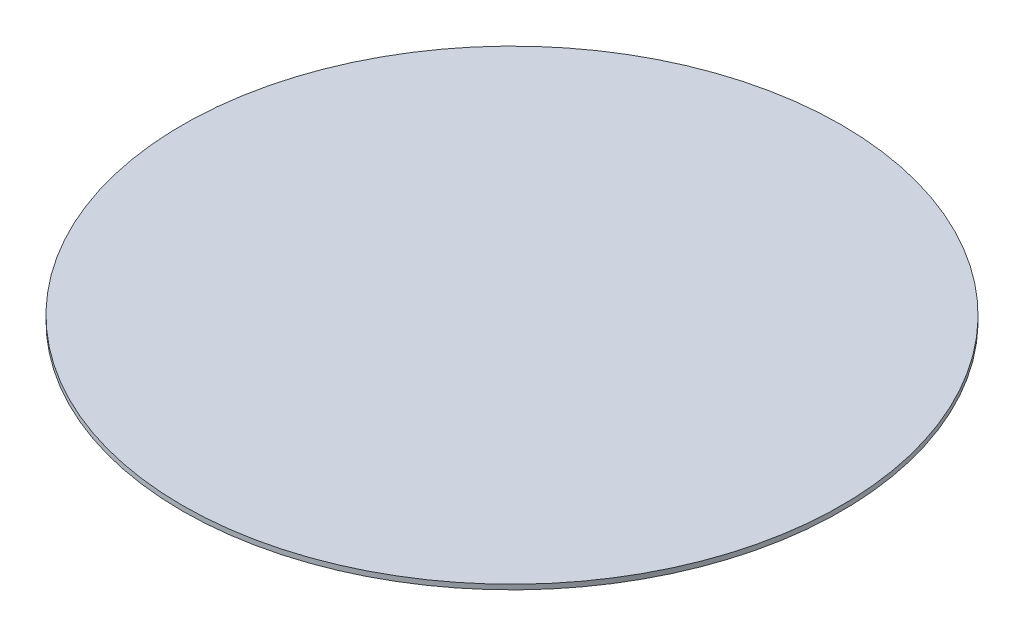
SolidWorks part; units mm, degrees
ref_plane "Front Plane" through (0, 0, 0) normal (0, 0, 1) x (1, 0, 0)
ref_plane "Top Plane" through (0, 0, 0) normal (0, 1, 0) x (1, 0, 0)
ref_plane "Right Plane" through (0, 0, 0) normal (1, 0, 0) x (0, 0, -1)
sketch "Sketch1" plane through (0, 0, 0) normal (0, 1, 0) x (1, 0, 0)
  circle A0 centre (0, 0) radius 67.5
  dimension "D1" = 135
extrude "Boss-Extrude1" add sketch "Sketch1" along normal blind 1
